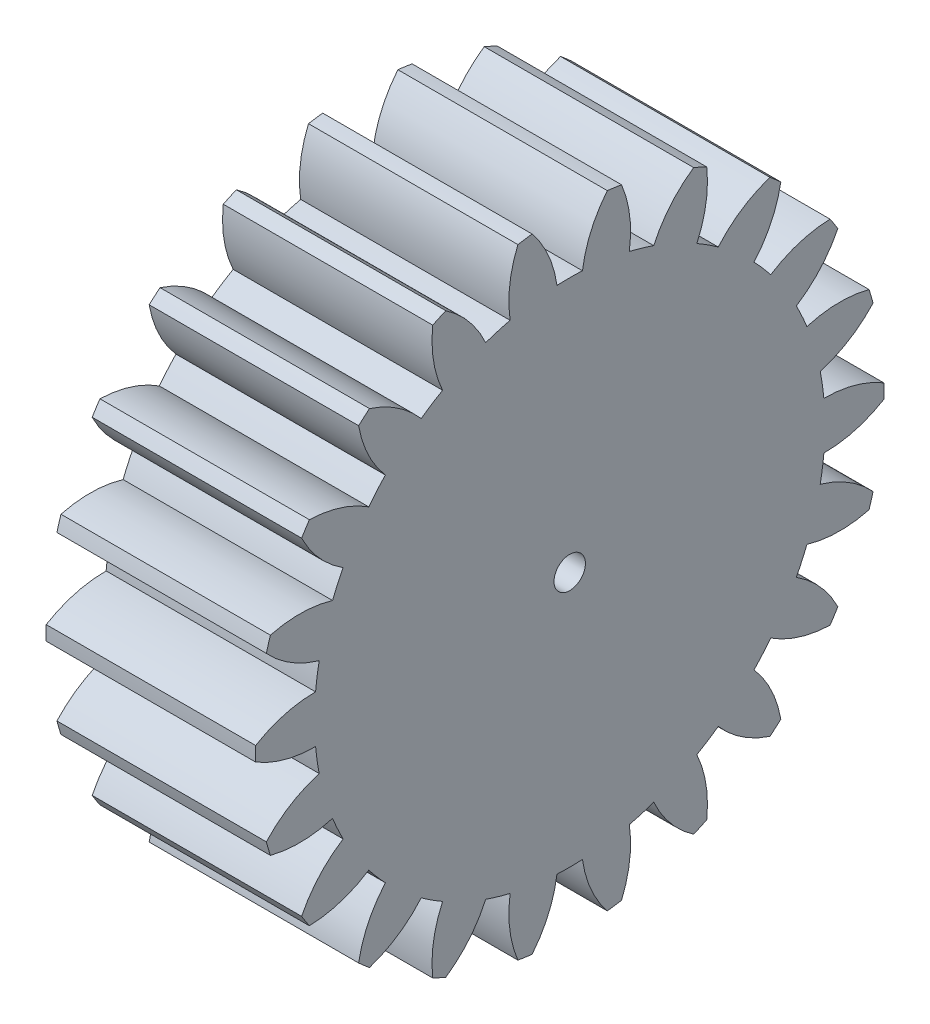
SolidWorks part; units mm, degrees
ref_plane "Plane1" through (0, 0, 0) normal (0, 0, 1) x (1, 0, 0)
ref_plane "Plane2" through (0, 0, 0) normal (0, 1, 0) x (1, 0, 0)
ref_plane "Plane3" through (0, 0, 0) normal (1, 0, 0) x (0, 0, -1)
sketch "HoldingSke" plane through (0, 0, 0) normal (0, 1, 0) x (1, 0, 0)
  line L0 (0, 0) -> (0.3709, -0.1498)
  line L1 (-15, 0) -> (100, 0) construction
  line L2 (0, 0) -> (-2.1039, 2.3779)
  line L3 (0, 0) -> (-11.863, 4.5341)
  line L4 (0, 0) -> (8.0072, 3.2351)
  line L5 (0, 0) -> (-46.8476, -17.4728)
  line L6 (0, 0) -> (-16.5793, -11.1861)
  line L7 (-2.1039, 2.3779) -> (8.6586, 51.2059)
  line L8 (-76.2, 54.61) -> (-75.7, 54.61)
  line L9 (-71.009, 38.7566) -> (-53.1078, 45.2721)
  line L10 (-76.2, 71.12) -> (104.1128, 71.12)
  line L11 (0, 0) -> (-20, 0)
  line L12 (-76.2, 101.6) -> (-76.113, 101.6)
  line L13 (24.9733, 27.94) -> (52.9518, 28.4284)
  line L14 (24.9733, 27.94) -> (24.9743, 27.94)
  line L15 (24.9733, 27.94) -> (100.4006, 29.5858)
  line L16 (-63.627, -2.5) -> (-12.827, -2.5)
  circle A0 centre (0, 0) radius 1.5
  circle A1 centre (0, 0) radius 24.374
  circle A2 centre (0, 0) radius 37.5
  circle A3 centre (0, 0) radius 1.5
  dimension "MHD" = 48.748
  dimension "Hub_dia" = 75
  dimension "Bore" = 3
  dimension "MBD" = 3
  dimension "Num_teeth" = 22
  dimension "Pitch" = 0.4
  dimension "Overall_len" = 50
  dimension "Show_teeth" = 22
  dimension "Thickness" = 20
  dimension "OAL" = 50.0001
  dimension "T_dim" = 0.5
  dimension "Ap" = 20
  dimension "H" = 19.05
  dimension "Pitch_radius" = 180.3128
  dimension "Width" = 20
  dimension "Backlash" = 0.087
  dimension "Addendum_fac" = 1
  dimension "Dedendum_fac" = 1.25
  dimension "Clearance_fac" = 0.25
  dimension "Dedendum_add" = 0.001
  dimension "Module" = 2.5
sketch "BasProSke" plane through (0, 0, 0) normal (0, 1, 0) x (1, 0, 0)
  line L0 (-10, 0) -> (60, 0) construction
  line L1 (0, 0) -> (0, 30)
  line L2 (0, 0) -> (20, 0)
  line L3 (20, 0) -> (20, 30)
  line L4 (20, 30) -> (0, 30)
  dimension "Thickness" = 20
  dimension "Diameter" = 60
revolve "Base-Revolve" add sketch "BasProSke" angle 360 about L0
sketch "TooCutSke" plane through (0, 0, 0) normal (1, 0, 0) x (0, 0, -1)
  line L1 (0, 0) -> (0, 107) construction
  line L2 (0, 0) -> (-2.114, 27.4186) construction
  line L3 (0, 0) -> (-7.8104, 54.3222) construction
  line L4 (-2.114, 27.4186) -> (-3.9052, 27.1611) construction
  arc A0 (1.2153, 24.3437) -> (-1.2153, 24.3437) centre (0, 0) ccw
  arc A1 (3.6084, 29.8078) -> (-3.6084, 29.8078) centre (0, 0) ccw
  circle A2 centre (0, 0) radius 27.5 construction
  circle A3 centre (0, 0) radius 25.8415 construction
  arc A4 (-1.2153, 24.3437) -> (-3.6084, 29.8078) centre (-12.1104, 22.8281) ccw
  arc A5 (3.6084, 29.8078) -> (1.2153, 24.3437) centre (12.1104, 22.8281) ccw
  dimension "Root_dia" = 48.748
  dimension "Overcut_dia" = 60.0508
  dimension "Pitch_dia" = 55
  dimension "Base_dia" = 51.6831
  dimension "Flank_rad" = 11
  dimension "Half_ang" = 8.182
  dimension "Half_CT" = 1.8096
extrude "ToothCut" cut sketch "TooCutSke" along normal through all
fillet "Breaks" [suppressed] radius 0.05
fillet "RootFillets" [suppressed] radius 0.626
pattern_circular "TeethCuts" count 22 every 16.364 about axis through (-10, 0, 0) along (1, 0, 0) of "ToothCut", "RootFillets", "Breaks"
sketch "HubNeaOneSke" plane through (0, 0, 0) normal (-1, 0, 0) x (0, 0, 1)
  circle A0 centre (0, 0) radius 24.374
  dimension "Diameter" = 48.748
extrude "HubNearOne" [suppressed] add sketch "HubNeaOneSke" along normal blind 30.0001
sketch "HubNeaBotSke" plane through (0, 0, 0) normal (-1, 0, 0) x (0, 0, 1)
  circle A0 centre (0, 0) radius 24.374
  dimension "Diameter" = 48.748
extrude "HubNearBoth" [suppressed] add sketch "HubNeaBotSke" along normal blind 15
ref_plane "FarPln" through (20, 0, 0) normal (1, 0, 0) x (0, 0, -1)
sketch "HubFarSke" plane through (20, 0, 0) normal (1, 0, 0) x (0, 0, -1)
  circle A0 centre (0, 0) radius 24.374
  dimension "Diameter" = 48.748
extrude "HubFar" [suppressed] add sketch "HubFarSke" along normal blind 15
sketch "BorSke" plane through (0, 0, 0) normal (1, 0, 0) x (0, 0, -1)
  circle A0 centre (0, 0) radius 1.5
  dimension "Diameter" = 3
extrude "Bore" cut sketch "BorSke" along normal mid plane 100.0001
sketch "KeySke" plane through (0, 0, 0) normal (1, 0, 0) x (0, 0, -1)
  line L0 (-0.6, 0) -> (-0.6, 2)
  line L1 (-0.6, 2) -> (0.6, 2)
  line L2 (0.6, 2) -> (0.6, 0)
  line L3 (0, 0) -> (0, 34) construction
  line L4 (-0.6, 0) -> (0.6, 0)
  dimension "Offset" = 2
  dimension "Width" = 1.2
extrude "Keyway" [suppressed] cut sketch "KeySke" along normal mid plane 100.0001
pattern_circular "Keyway2" [suppressed] count 2 every 90 about axis through (-10, 0, 0) along (1, 0, 0)
equation "' \"Module@HoldingSke\" = 6.35"
equation "' \"Num_teeth@HoldingSke\" = 12"
equation "' \"Ap@HoldingSke\" =  20"
equation "' \"Ap@HoldingSke\" = 20"
equation "' \"Width@HoldingSke\" = 0.5 * 25.4"
equation "' \"Hub_dia@HoldingSke\"= 1 * 25.4"
equation "' \"Hub_dia@HoldingSke\" = 1 * 25.4"
equation "' \"Overall_len@HoldingSke\" = 1.0 * 25.4"
equation "' \"Bore@HoldingSke\" = 0.75 * 25.4"
equation "' \"T_dim@HoldingSke\" = 0.1 * 25.4"
equation "' \"Width@KeySke\" = 0.25 * 25.4"
equation "' \"Show_teeth@HoldingSke\" = 13"
equation "' \"Backlash@HoldingSke\" = 0.009 * 25.4"
equation "' \"Addendum_fac@HoldingSke\" = 1.0"
equation "' \"Dedendum_fac@HoldingSke\" = 1.25"
equation "' \"Dedendum_add@HoldingSke\" = 0.00005 * 25.4"
equation "' \"Clearance_fac@HoldingSke\" = 0.25"
equation "\"Pitch@HoldingSke\" = 1 / \"Module@HoldingSke\""
equation "\"Overcut_dia@TooCutSke\" = (\"Num_teeth@HoldingSke\" + 2 * \"Addendum_fac@HoldingSke\") / \"Pitch@HoldingSke\" + 0.002 * 25.4"
equation "\"Pitch_dia@TooCutSke\" = \"Num_teeth@HoldingSke\" / \"Pitch@HoldingSke\""
equation "\"Base_dia@TooCutSke\" = \"Num_teeth@HoldingSke\" / \"Pitch@HoldingSke\" * cos((\"Ap@HoldingSke\"  * 3.14159265 / 180))"
equation "\"Root_dia@TooCutSke\" = (\"Num_teeth@HoldingSke\" + 2) / \"Pitch@HoldingSke\" - 2 * (\"Addendum_fac@HoldingSke\" + \"Dedendum_fac@HoldingSke\") / \"Pitch@HoldingSke\" - \"Dedendum_add@HoldingSke\" * 2"
equation "\"Half_ang@TooCutSke\" = 180 / \"Num_teeth@HoldingSke\""
equation "\"Half_CT@TooCutSke\" = \"Num_teeth@HoldingSke\" / \"Pitch@HoldingSke\" * sin((3.14159265 / 2 / \"Num_teeth@HoldingSke\")) / 2 - 7 * \"Backlash@HoldingSke\" / 4"
equation "\"Flank_rad@TooCutSke\" = \"Num_teeth@HoldingSke\" / \"Pitch@HoldingSke\" / 5"
equation "\"Radius@RootFillets\" = \"Clearance_fac@HoldingSke\" / \"Pitch@HoldingSke\" + \"Dedendum_add@HoldingSke\""
equation "\"Break_rad@Breaks\" = 0.02 / \"Pitch@HoldingSke\""
equation "\"Thickness@HoldingSke\" = \"Width@HoldingSke\""
equation "\"OAL@HoldingSke\" = \"Thickness@HoldingSke\""
equation "\"MHD@HoldingSke\" = (\"Num_teeth@HoldingSke\" + 2) / \"Pitch@HoldingSke\" - 2 * (\"Addendum_fac@HoldingSke\" + \"Dedendum_fac@HoldingSke\")  / \"Pitch@HoldingSke\" - \"Dedendum_add@HoldingSke\" * 2"
equation "\"MBD@HoldingSke\" = (\"Num_teeth@HoldingSke\" + 2) / \"Pitch@HoldingSke\" - 2 * (\"Addendum_fac@HoldingSke\" + \"Dedendum_fac@HoldingSke\")  / \"Pitch@HoldingSke\" - \"Dedendum_add@HoldingSke\" * 2 - 0.002 * 25.4"
equation "\"MHD@HoldingSke\" = ((sgn( \"MHD@HoldingSke\" - \"Hub_dia@HoldingSke\" )-1)*( \"MHD@HoldingSke\" - \"Hub_dia@HoldingSke\" ))/-2+ \"Hub_dia@HoldingSke\""
equation "\"MBD@HoldingSke\" = ((sgn( \"MBD@HoldingSke\" - \"Bore@HoldingSke\" )-1)*( \"MBD@HoldingSke\" - \"Bore@HoldingSke\" ))/-2+ \"Bore@HoldingSke\""
equation "\"OAL@HoldingSke\" = ((sgn( \"OAL@HoldingSke\" - \"Overall_len@HoldingSke\" )+1)*( \"OAL@HoldingSke\" - \"Overall_len@HoldingSke\" ))/2 + \"Overall_len@HoldingSke\" + 0.000002 * 25.4"
equation "\"Num_teeth@TeethCuts\" = int( \"Show_teeth@HoldingSke\" ) + 1"
equation "\"Num_teeth@TeethCuts\" = ((sgn( \"Num_teeth@TeethCuts\" - \"Num_teeth@HoldingSke\" )-1)*( \"Num_teeth@TeethCuts\" - \"Num_teeth@HoldingSke\" ))/-2+ \"Num_teeth@HoldingSke\""
equation "\"Num_teeth@TeethCuts\" = ((sgn( \"Num_teeth@TeethCuts\" - 2.0)+1)*( \"Num_teeth@TeethCuts\" - 2.0))/2 +2.0"
equation "\"Angle@TeethCuts\" = 360.0 / \"Num_teeth@HoldingSke\""
equation "\"Diameter@BasProSke\" = (\"Num_teeth@HoldingSke\" + 2 * \"Addendum_fac@HoldingSke\") / \"Pitch@HoldingSke\""
equation "\"Thickness@BasProSke\"  = \"Thickness@HoldingSke\""
equation "' \"Fillet_rad@BasProSke\" =  \"Thickness@HoldingSke\" * 0.05"
equation "' \"Fillet_rad@BasProSke\" = \"Thickness@HoldingSke\" * 0.05"
equation "\"MHD@HoldingSke\" = ((sgn( \"MHD@HoldingSke\" - \"Root_dia@TooCutSke\" )-1)*( \"MHD@HoldingSke\" - \"Root_dia@TooCutSke\" ))/-2+ \"Root_dia@TooCutSke\""
equation "\"Diameter@HubNeaOneSke\" = \"MHD@HoldingSke\""
equation "\"Length@HubNearOne\" = \"OAL@HoldingSke\" - \"Thickness@BasProSke\""
equation "\"Diameter@HubNeaBotSke\" = \"MHD@HoldingSke\""
equation "\"Length@HubNearBoth\" = ( \"OAL@HoldingSke\" - \"Thickness@BasProSke\" ) / 2.0"
equation "\"Thickness@FarPln\" = \"Thickness@BasProSke\""
equation "\"Diameter@HubFarSke\" = \"MHD@HoldingSke\""
equation "\"Length@HubFar\" = ( \"OAL@HoldingSke\" - \"Thickness@BasProSke\" ) / 2.0"
equation "\"Diameter@BorSke\" = \"MBD@HoldingSke\""
equation "\"D1@Bore\" = \"OAL@HoldingSke\" * 2.0"
equation "\"D1@Keyway\" = \"OAL@HoldingSke\" * 2.0"
equation "\"Offset@KeySke\" = \"T_dim@HoldingSke\" + \"MBD@HoldingSke\" / 2.0"
